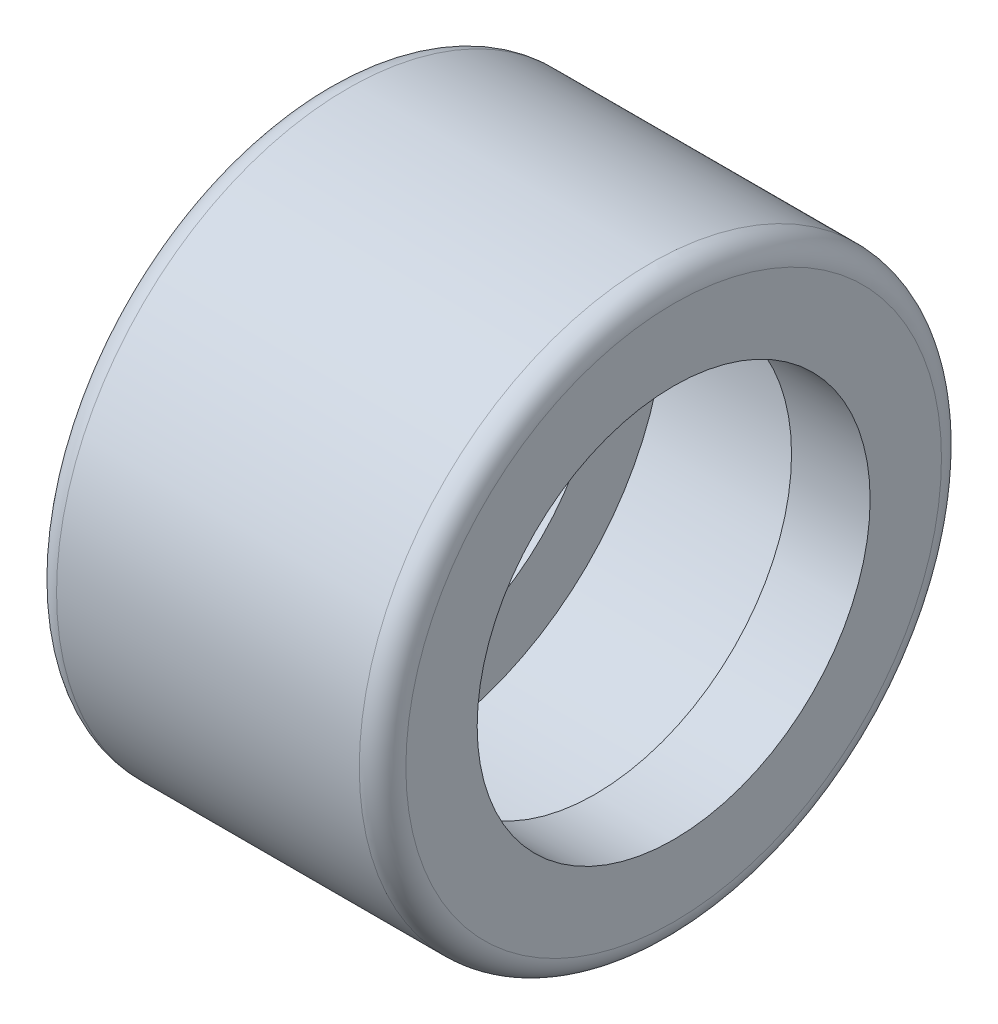
SolidWorks part; units mm, degrees
ref_plane "Front Plane" through (0, 0, 0) normal (0, 0, 1) x (1, 0, 0)
ref_plane "Top Plane" through (0, 0, 0) normal (0, 1, 0) x (1, 0, 0)
ref_plane "Right Plane" through (0, 0, 0) normal (1, 0, 0) x (0, 0, -1)
ref_plane "Plane1" through (0, 0, 0) normal (0, 0, 1) x (1, 0, 0)
sketch "Sketch1" plane through (0, 0, 0) normal (0, 0, 1) x (1, 0, 0)
  line L0 (0, 4.6) -> (0, 3.375)
  line L1 (0, 3.375) -> (1.35, 3.375)
  line L2 (1.35, 3.375) -> (1.35, 4.5)
  line L3 (1.35, 4.5) -> (4.65, 4.5)
  line L4 (4.65, 4.5) -> (4.65, 3.375)
  line L5 (4.65, 3.375) -> (6, 3.375)
  line L6 (6, 3.375) -> (6, 4.6)
  line L7 (5.6, 5) -> (0.4, 5)
  line L8 (50, 0) -> (-50, 0) construction
  arc A0 (6, 4.6) -> (5.6, 5) centre (5.6, 4.6) ccw
  arc A1 (0.4, 5) -> (0, 4.6) centre (0.4, 4.6) ccw
revolve "Revolve1" add sketch "Sketch1" angle 360 about L8
